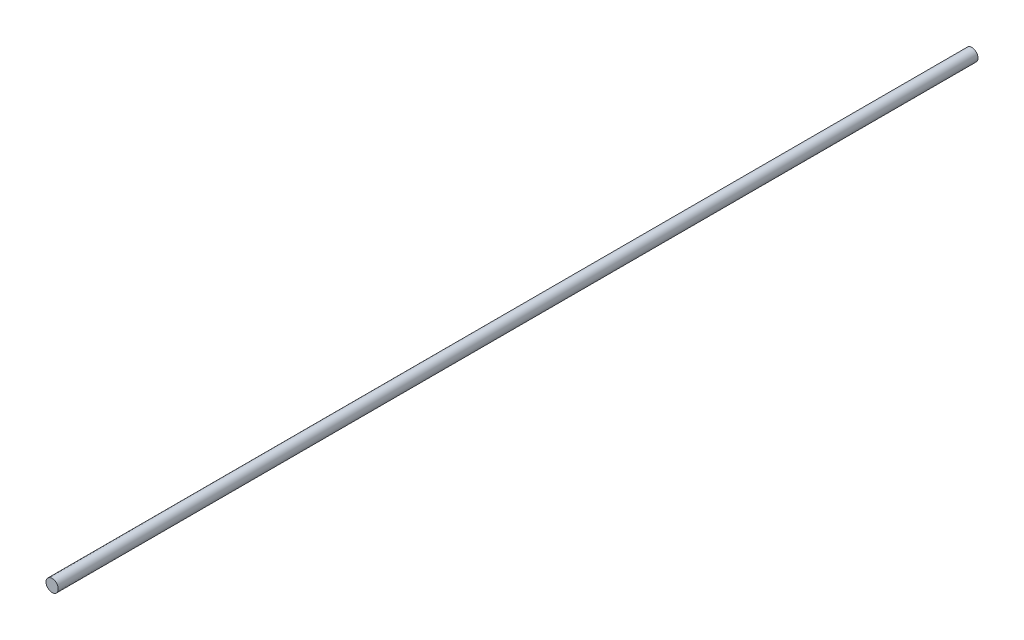
SolidWorks part; units mm, degrees
material "Plain Carbon Steel"
ref_plane "Front Plane" through (0, 0, 0) normal (0, 0, 1) x (1, 0, 0)
ref_plane "Top Plane" through (0, 0, 0) normal (0, 1, 0) x (1, 0, 0)
ref_plane "Right Plane" through (0, 0, 0) normal (1, 0, 0) x (0, 0, -1)
sketch "Sketch1" plane through (0, 0, 0) normal (0, 0, 1) x (1, 0, 0)
  circle A0 centre (0, 0) radius 4
  dimension "D1" = 8
extrude "Boss-Extrude1" add sketch "Sketch1" along normal blind 600
